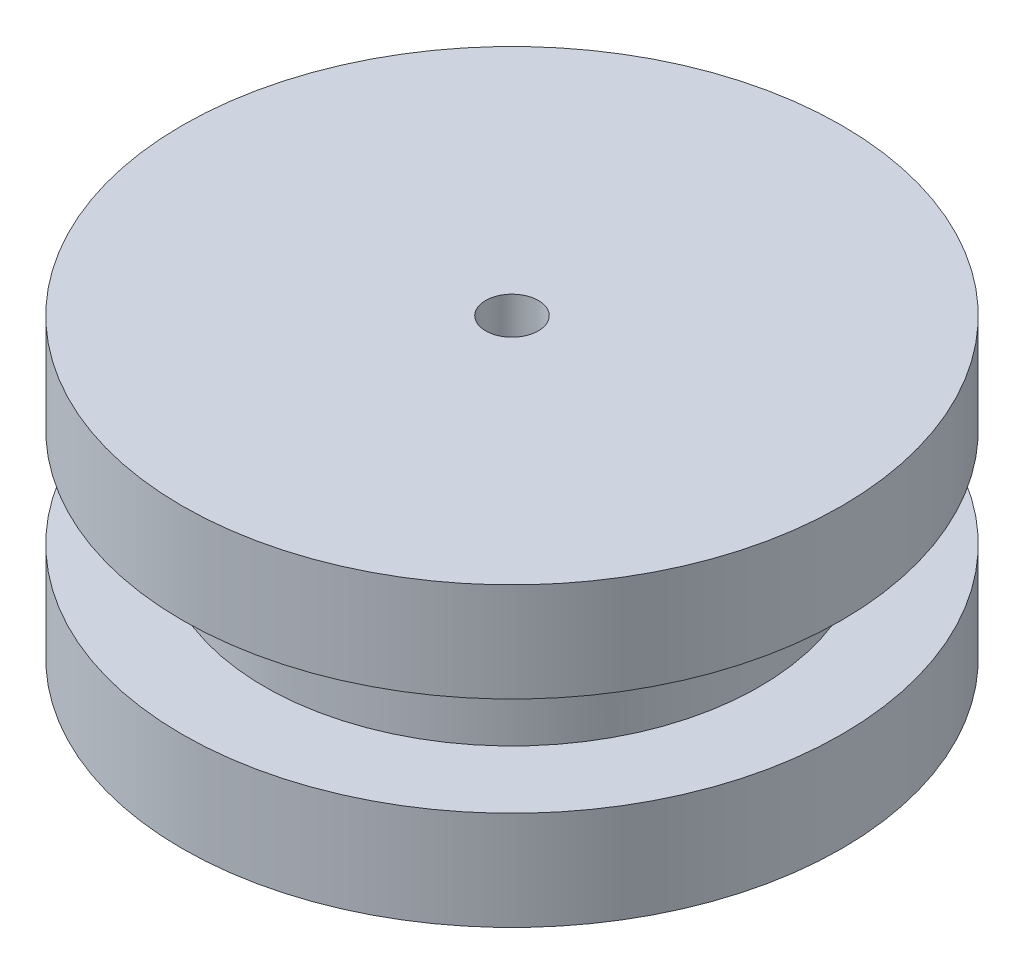
SolidWorks part; units mm, degrees
ref_plane "Front Plane" through (0, 0, 0) normal (0, 0, 1) x (1, 0, 0)
ref_plane "Top Plane" through (0, 0, 0) normal (0, 1, 0) x (1, 0, 0)
ref_plane "Right Plane" through (0, 0, 0) normal (1, 0, 0) x (0, 0, -1)
sketch "Sketch1" plane through (0, 0, 0) normal (0, 1, 0) x (1, 0, 0)
  circle A0 centre (0, 0) radius 11.25
extrude "Boss-Extrude1" add sketch "Sketch1" along normal blind 4.5
sketch "Sketch2" plane through (0, 4.5, 0) normal (0, 1, 0) x (1, 0, 0)
  circle A0 centre (0, 0) radius 15
extrude "Boss-Extrude2" add sketch "Sketch2" along normal blind 4.5
sketch "Sketch3" plane through (0, 0, 0) normal (0, -1, 0) x (-1, 0, 0)
  circle A0 centre (0, 0) radius 15
extrude "Boss-Extrude3" add sketch "Sketch3" along normal blind 4.5
hole_wizard "M2 Clearance Hole1" positions "Sketch7" profile "Sketch8" hole size "M2" standard "ANSI Metric" end condition through all
sketch "Sketch7" plane through (0, -4.5, 0) normal (0, -1, 0) x (-1, 0, 0)
  point P0 (0, 0)
sketch "Sketch8" plane through (0, -4.5, 0) normal (1, 0, 0) x (0, 0, -1)
  line L0 (0, 0) -> (0, 13.5)
  line L1 (0, 13.5) -> (1.2, 13.5)
  line L2 (1.2, 13.5) -> (1.2, 0)
  line L5 (1.2, 0) -> (0, 0)
  line L11 (0, -6.35) -> (0, 107.95) construction
  dimension "Thru Hole Dia." = 2.4
  dimension "Thru Hole Depth" = 13.5
